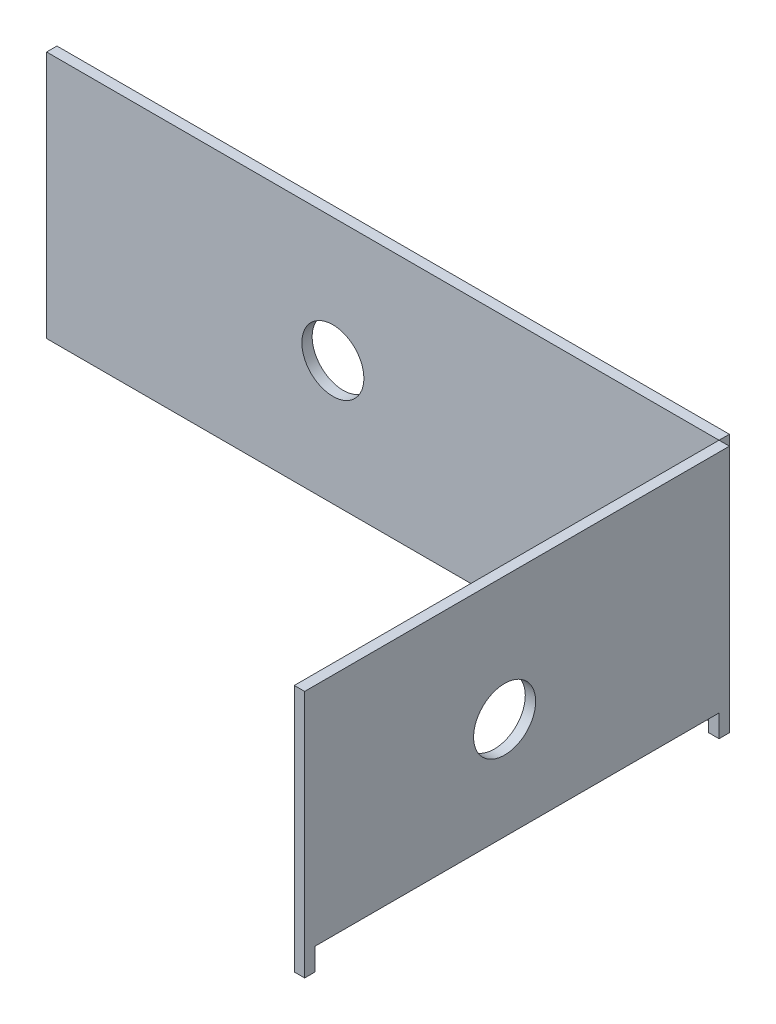
SolidWorks part; units mm, degrees
ref_plane "Front Plane" through (0, 0, 0) normal (0, 0, 1) x (1, 0, 0)
ref_plane "Top Plane" through (0, 0, 0) normal (0, 1, 0) x (1, 0, 0)
ref_plane "Right Plane" through (0, 0, 0) normal (1, 0, 0) x (0, 0, -1)
sketch "Sketch2" plane through (0, 0, 0) normal (0, 0, 1) x (1, 0, 0)
  line L0 (-33.735, 0) -> (160.0162, 0)
  line L1 (160.0162, 0) -> (166.3662, 0)
  line L2 (-33.735, 0) -> (-40.085, 0)
  line L6 (-40.085, 0) -> (-40.085, -76.2)
  line L7 (-40.085, -76.2) -> (166.3662, -76.2)
  line L8 (166.3662, -76.2) -> (166.3662, 0)
  circle A0 centre (47.799, -38.1) radius 9.525
extrude "Boss-Extrude3" add sketch "Sketch2" along normal blind 3.175 contours A0 | L2 L6 L7 L8 L1 L0
sketch "Sketch9" plane through (166.3662, 0, 0) normal (1, 0, 0) x (0, 0, -1)
  line L0 (-3.175, 0) -> (-133.5786, 0)
  line L1 (-3.175, 0) -> (-3.175, -76.2)
  line L2 (-3.175, -76.2) -> (-6.35, -76.2)
  line L3 (-6.35, -76.2) -> (-6.35, -69.342)
  line L4 (-6.35, -69.342) -> (-130.4036, -69.342)
  line L5 (-130.4036, -69.342) -> (-130.4036, -76.2)
  line L8 (-130.4036, -76.2) -> (-133.5786, -76.2)
  line L9 (-133.5786, -76.2) -> (-133.5786, 0)
  circle A0 centre (-72.1868, -38.1) radius 9.525
extrude "Boss-Extrude5" add sketch "Sketch9" along normal blind 3.175 separate body
